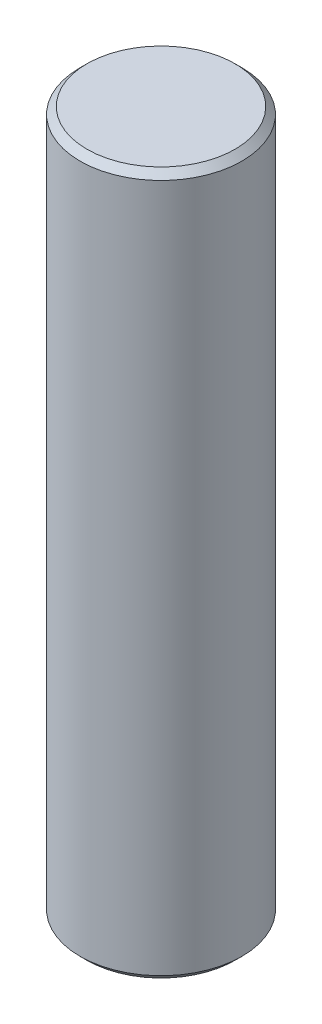
SolidWorks part; units mm, degrees
ref_plane "Front Plane" through (0, 0, 0) normal (0, 0, 1) x (1, 0, 0)
ref_plane "Top Plane" through (0, 0, 0) normal (0, 1, 0) x (1, 0, 0)
ref_plane "Right Plane" through (0, 0, 0) normal (1, 0, 0) x (0, 0, -1)
sketch "Sketch1" plane through (0, 0, 0) normal (0, 1, 0) x (1, 0, 0)
  circle A0 centre (0, 0) radius 2.95
  dimension "D1" = 5.9
extrude "Boss-Extrude1" add sketch "Sketch1" against normal blind 25.6
chamfer "Chamfer3" distance 0.25 angle 45 1 edges at (0, -25.6, 2.95)
chamfer "Chamfer4" distance 0.25 angle 45 1 edges at (0, 0, 2.95)
